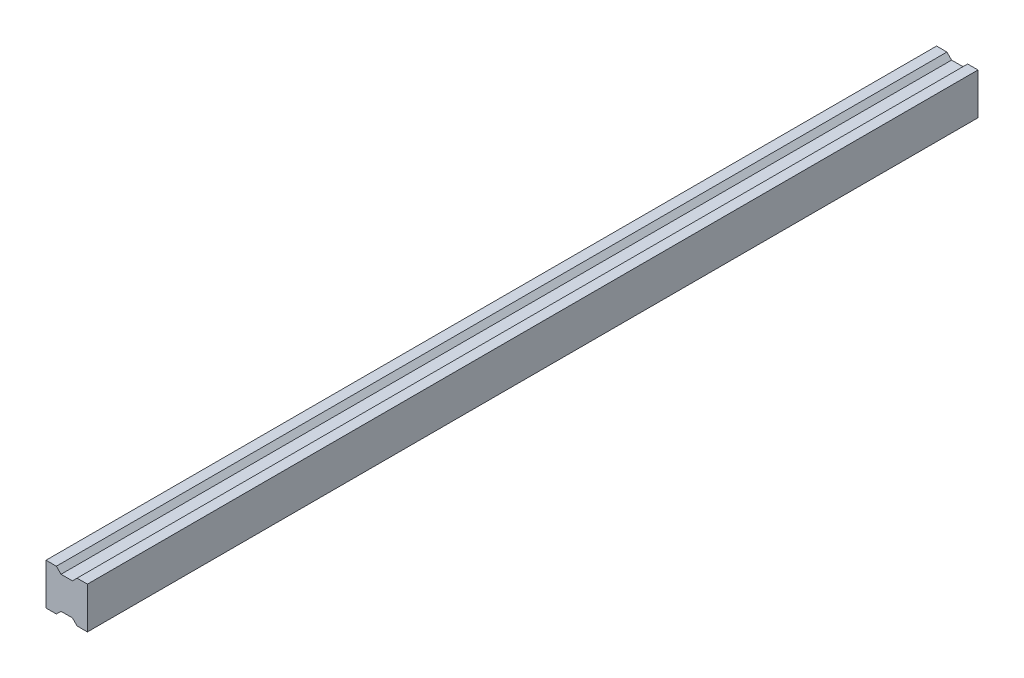
SolidWorks part; units mm, degrees
ref_plane "Front Plane" through (0, 0, 0) normal (0, 0, 1) x (1, 0, 0)
ref_plane "Top Plane" through (0, 0, 0) normal (0, 1, 0) x (1, 0, 0)
ref_plane "Right Plane" through (0, 0, 0) normal (1, 0, 0) x (0, 0, -1)
sketch "Sketch1" plane through (0, 0, 0) normal (0, 0, 1) x (1, 0, 0)
  line L0 (-2.75, -7.75) -> (2.75, -7.75)
  line L1 (2.75, -7.75) -> (5, -10)
  line L2 (5, -10) -> (10, -10)
  line L3 (10, -10) -> (10, 10)
  line L4 (10, 10) -> (5, 10)
  line L5 (5, 10) -> (2.75, 7.75)
  line L6 (2.75, 7.75) -> (-2.75, 7.75)
  line L7 (-2.75, 7.75) -> (-5, 10)
  line L8 (-5, 10) -> (-10, 10)
  line L9 (-10, 10) -> (-10, -10)
  line L10 (-10, -10) -> (-5, -10)
  line L11 (-5, -10) -> (-2.75, -7.75)
  dimension "D1" = 2.75
  dimension "D2" = 10
  dimension "D3" = 2.75
  dimension "D4" = 5
  dimension "D5" = 10
extrude "Boss-Extrude1" add sketch "Sketch1" along normal blind 430
